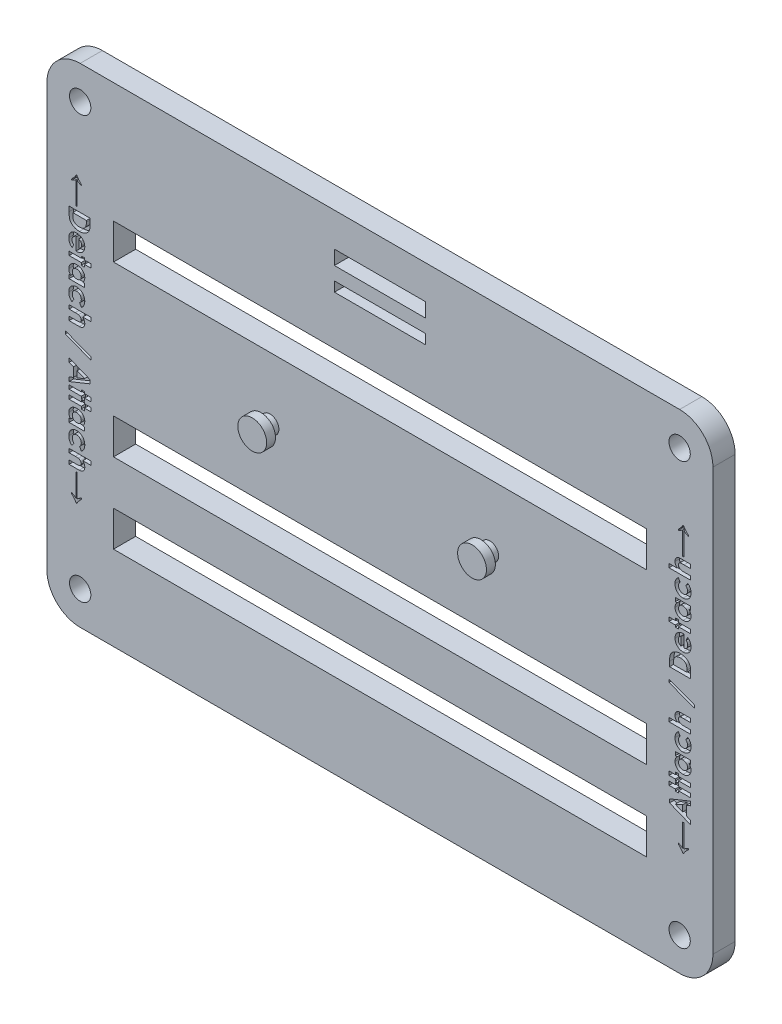
SolidWorks part; units mm, degrees
material "ABS"
ref_plane "正面" through (0, 0, 0) normal (1, 0, 0) x (0, 1, 0)
ref_plane "平面" through (0, 0, 0) normal (0, 0, 1) x (0, 1, 0)
ref_plane "右側面" through (0, 0, 0) normal (0, 1, 0) x (-1, 0, 0)
sketch "ｽｹｯﾁ1" plane through (0, 0, 0) normal (0, 0, 1) x (0, 1, 0)
  line L1 (0, 0) -> (110, 0)
  line L2 (0, 0) -> (0, 150)
  line L3 (0, 150) -> (110, 150)
  line L4 (110, 0) -> (110, 150)
  dimension "D1" = 110
  dimension "D2" = 150
extrude "ﾎﾞｽ - 押し出し1" add sketch "ｽｹｯﾁ1" along normal blind 5
sketch "ｽｹｯﾁ5" plane through (0, 0, 5) normal (0, 0, 1) x (1, 0, 0)
  line L0 (-150, 55) -> (0, 55) construction
  line L1 (-150, 110) -> (-150, 0) construction
  line L2 (0, 0) -> (0, 110) construction
  line L3 (-99.75, 61) -> (-50.25, 61) construction
  circle A0 centre (-99.75, 61) radius 2
  circle A1 centre (-50.25, 61) radius 2
  point P4 (-75, 61)
  point P11 (-75, 55)
  dimension "D1" = 4
  dimension "D2" = 4
  dimension "D3" = 49.5
  dimension "D4" = 6
extrude "ﾎﾞｽ - 押し出し2" add sketch "ｽｹｯﾁ5" along normal blind 2
sketch "ｽｹｯﾁ6" plane through (0, 0, 7) normal (0, 0, 1) x (1, 0, 0)
  circle A0 centre (-99.75, 61) radius 3.25
  circle A1 centre (-50.25, 61) radius 3.25
  dimension "D1" = 6.5
extrude "ﾎﾞｽ - 押し出し3" add sketch "ｽｹｯﾁ6" along normal blind 2
sketch "ｽｹｯﾁ2" plane through (0, 0, 5) normal (0, 0, 1) x (1, 0, 0)
  line L0 (-150, 110) -> (-150, 0) construction
  line L1 (-142.5, 102.5) -> (-7.5, 102.5) construction
  line L2 (-142.5, 102.5) -> (-142.5, 7.5) construction
  line L3 (-142.5, 7.5) -> (-7.5, 7.5) construction
  line L4 (-7.5, 102.5) -> (-7.5, 7.5) construction
  line L5 (0, 110) -> (-150, 110) construction
  point P11 (-142.5, 102.5)
  point P14 (-142.5, 7.5)
  point P17 (-7.5, 7.5)
  point P20 (-7.5, 102.5)
  dimension "D1" = 135
  dimension "D2" = 7.5
  dimension "D3" = 95
  dimension "D4" = 7.5
hole_wizard "M4 すきま穴1" positions "ｽｹｯﾁ2" profile "ｽｹｯﾁ3" hole size "M4" standard "JIS" end condition through all
sketch "ｽｹｯﾁ3" plane through (-7.5, 102.5, 5) normal (1, 0, 0) x (0, -1, 0)
  line L0 (0, 0) -> (0, 5)
  line L1 (0, 5) -> (2.4, 5)
  line L2 (2.4, 5) -> (2.4, 0)
  line L5 (2.4, 0) -> (0, 0)
  line L11 (0, -6.35) -> (0, 107.95) construction
  dimension "通し穴の直径" = 4.8
  dimension "通し穴の深さ" = 5
sketch "ｽｹｯﾁ7" plane through (0, 0, 5) normal (0, 0, 1) x (1, 0, 0)
  line L0 (0, 110) -> (-150, 110) construction
  line L1 (-85.25, 102.4) -> (-64.75, 102.4)
  line L2 (-85.25, 102.4) -> (-85.25, 99.2)
  line L3 (-85.25, 99.2) -> (-64.75, 99.2)
  line L4 (-64.75, 102.4) -> (-64.75, 99.2)
  line L5 (-85.25, 96.2) -> (-64.75, 96.2)
  line L6 (-85.25, 96.2) -> (-85.25, 94)
  line L7 (-85.25, 94) -> (-64.75, 94)
  line L8 (-64.75, 96.2) -> (-64.75, 94)
  line L9 (-150, 55) -> (0, 55) construction
  line L10 (-150, 110) -> (-150, 0) construction
  line L11 (0, 0) -> (0, 110) construction
  line L13 (-135, 83) -> (-15, 83)
  line L14 (-135, 83) -> (-135, 75)
  line L15 (-135, 75) -> (-15, 75)
  line L16 (-15, 83) -> (-15, 75)
  line L17 (-135, 45) -> (-15, 45)
  line L18 (-135, 45) -> (-135, 37)
  line L19 (-135, 37) -> (-15, 37)
  line L20 (-15, 45) -> (-15, 37)
  line L21 (-135, 27) -> (-15, 27)
  line L22 (-135, 27) -> (-135, 19)
  line L23 (-135, 19) -> (-15, 19)
  line L24 (-15, 27) -> (-15, 19)
  point P10 (-75, 110)
  point P11 (-75, 102.4)
  point P12 (-75, 96.2)
  point P31 (-75, 75)
  point P32 (-75, 55)
  point P33 (-75, 37)
  point P34 (-75, 19)
  dimension "D1" = 20.5
  dimension "D2" = 3.2
  dimension "D3" = 39
  dimension "D4" = 3
  dimension "D5" = 8
  dimension "D6" = 120
  dimension "D7" = 20
  dimension "D8" = 10
  dimension "D9" = 10
  dimension "D10" = 2.2
extrude "ｶｯﾄ - 押し出し1" cut sketch "ｽｹｯﾁ7" against normal through all
fillet "ﾌｨﾚｯﾄ1" radius 7.5 4 edges at (-150, 0, 2.5) (-150, 110, 2.5) (0, 110, 2.5) (0, 0, 2.5)
sketch "ｽｹｯﾁ8" plane through (0, 0, 5) normal (0, 0, 1) x (1, 0, 0)
  line L0 (-145, 95) -> (-145, 15) construction
  line L1 (-150, 102.5) -> (-150, 7.5) construction
  line L2 (-75, 110) -> (-75, 0) construction
  line L3 (-7.5, 110) -> (-142.5, 110) construction
  line L4 (-142.5, 0) -> (-7.5, 0) construction
  line L5 (-5, 95) -> (-5, 15) construction
  text T0 "<b>←Detach / Attach→</b>" font "Century Gothic" height in points 18
  text T1 "<b>←Attach / Detach→</b>" font "Century Gothic" height in points 18
  point P4 (-150, 55)
  point P5 (-145, 55)
  dimension "D1" = 5
  dimension "D2" = 80
extrude "ｶｯﾄ - 押し出し2" cut sketch "ｽｹｯﾁ8" against normal blind 1
